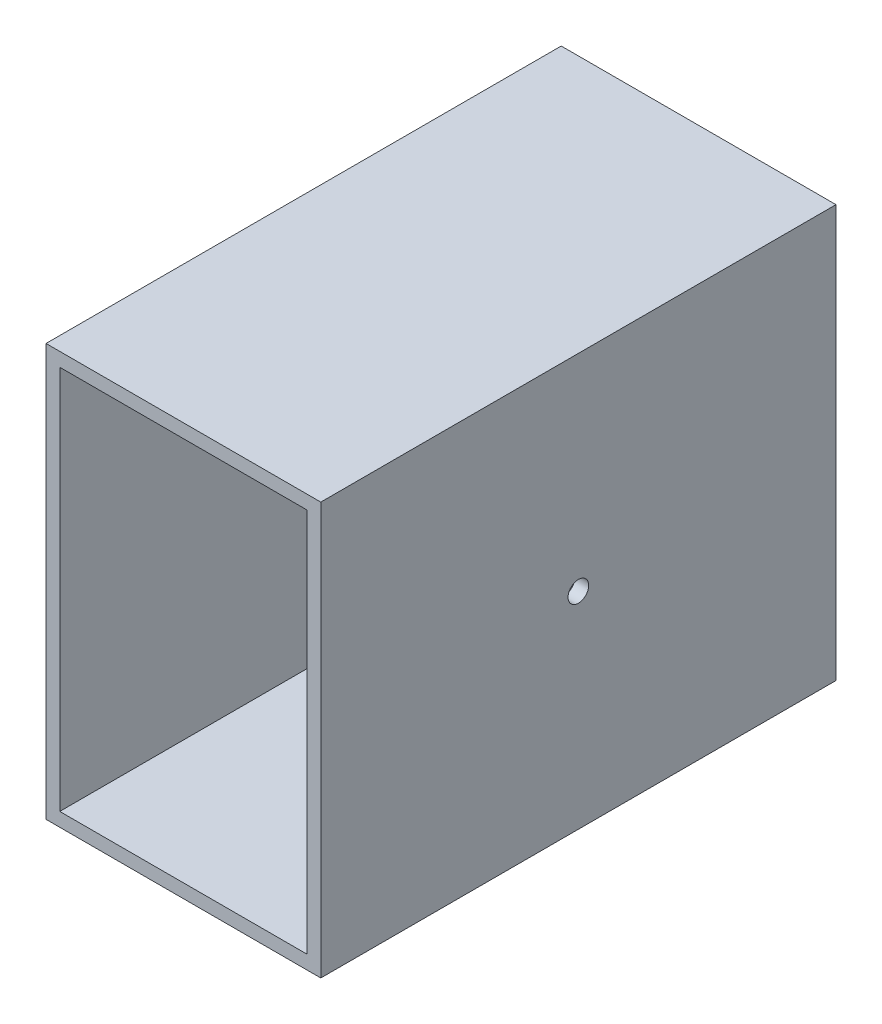
SolidWorks part; units mm, degrees
ref_plane "Front Plane" through (0, 0, 0) normal (0, 0, 1) x (1, 0, 0)
ref_plane "Top Plane" through (0, 0, 0) normal (0, 1, 0) x (1, 0, 0)
ref_plane "Right Plane" through (0, 0, 0) normal (1, 0, 0) x (0, 0, -1)
sketch "Sketch1" plane through (0, 0, 0) normal (0, 0, 1) x (1, 0, 0)
  line L1 (0, 0) -> (-72, 0)
  line L2 (0, 0) -> (0, 112)
  line L3 (0, 112) -> (-72, 112)
  line L4 (-72, 0) -> (-72, 112)
  line L5 (4, -4) -> (-76, -4)
  line L6 (4, -4) -> (4, 116)
  line L7 (4, 116) -> (-76, 116)
  line L8 (-76, -4) -> (-76, 116)
  dimension "D1" = 120
  dimension "D2" = 80
  dimension "D3" = 4
  dimension "D4" = 4
  dimension "D5" = 4
  dimension "D6" = 4
extrude "Boss-Extrude1" add sketch "Sketch1" along normal blind 150
sketch "Sketch2" plane through (4, 0, 0) normal (1, 0, 0) x (0, 0, -1)
  line L0 (0, -4) -> (0, 116) construction
  line L1 (-150, -4) -> (0, -4) construction
  circle A0 centre (-75, 56) radius 3
  dimension "D1" = 6
  dimension "D2" = 75
  dimension "D3" = 60
extrude "Cut-Extrude1" cut sketch "Sketch2" against normal blind 73
